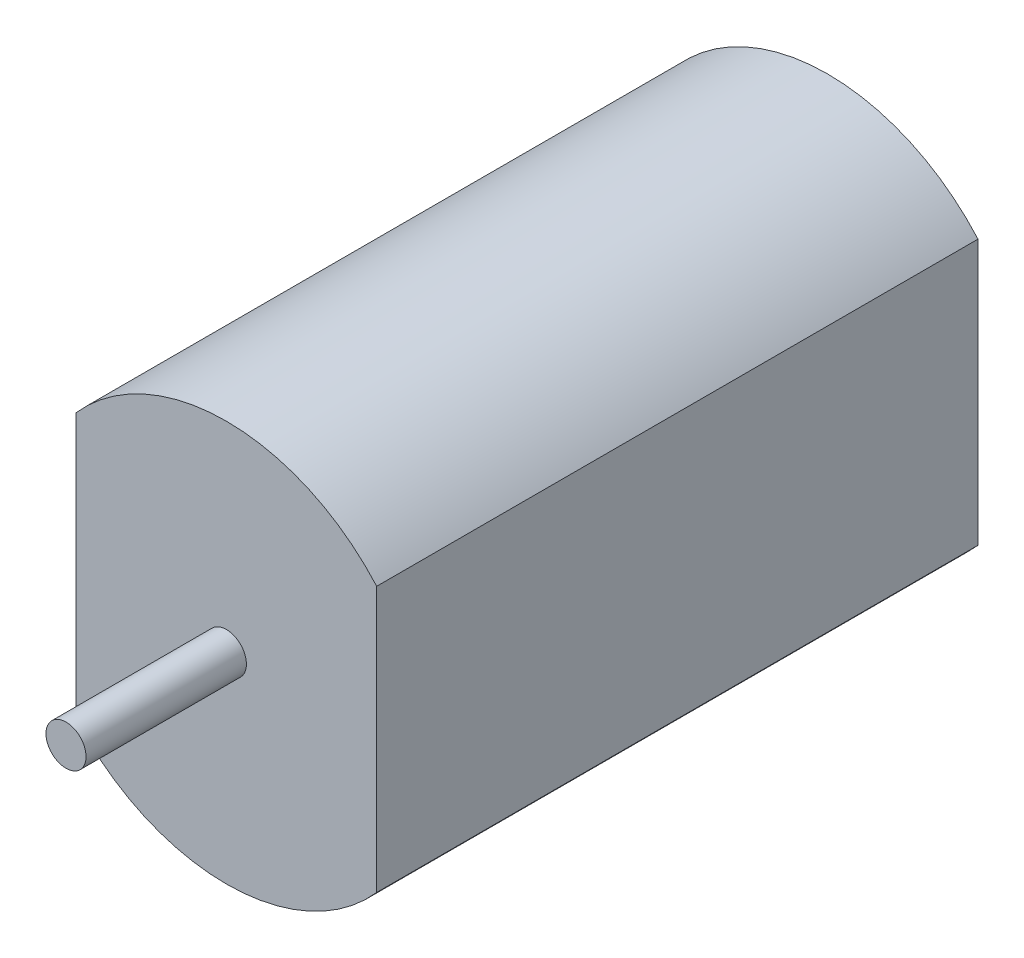
SolidWorks part; units mm, degrees
ref_plane "前视基准面" through (0, 0, 0) normal (0, 0, 1) x (1, 0, 0)
ref_plane "上视基准面" through (0, 0, 0) normal (0, 1, 0) x (1, 0, 0)
ref_plane "右视基准面" through (0, 0, 0) normal (1, 0, 0) x (0, 0, -1)
sketch "草图1" plane through (0, 0, 0) normal (0, 0, 1) x (1, 0, 0)
  circle A0 centre (0, 0) radius 10
  dimension "D1" = 20
extrude "凸台-拉伸1" add sketch "草图1" along normal blind 30
sketch "草图2" plane through (0, 0, 30) normal (0, 0, 1) x (1, 0, 0)
  line L0 (0, 4.7504) -> (0, -4.7504) construction
  line L1 (-7.5, 9.2129) -> (-7.5, -8.0325)
  line L2 (7.5, 9.2129) -> (7.5, -8.0325)
  circle A1 centre (0, 0) radius 10
  circle A2 centre (0, 0) radius 10
  circle M4 centre (0, 0) radius 10
  dimension "D2" = 15
  dimension "D1" = 0
extrude "切除-拉伸1" cut sketch "草图2" against normal blind 30 contours L2 M4 | L1 M4
sketch "草图3" plane through (0, 0, 30) normal (0, 0, 1) x (1, 0, 0)
  circle A0 centre (0, 0) radius 1
  dimension "D1" = 2
extrude "凸台-拉伸2" add sketch "草图3" along normal blind 8
